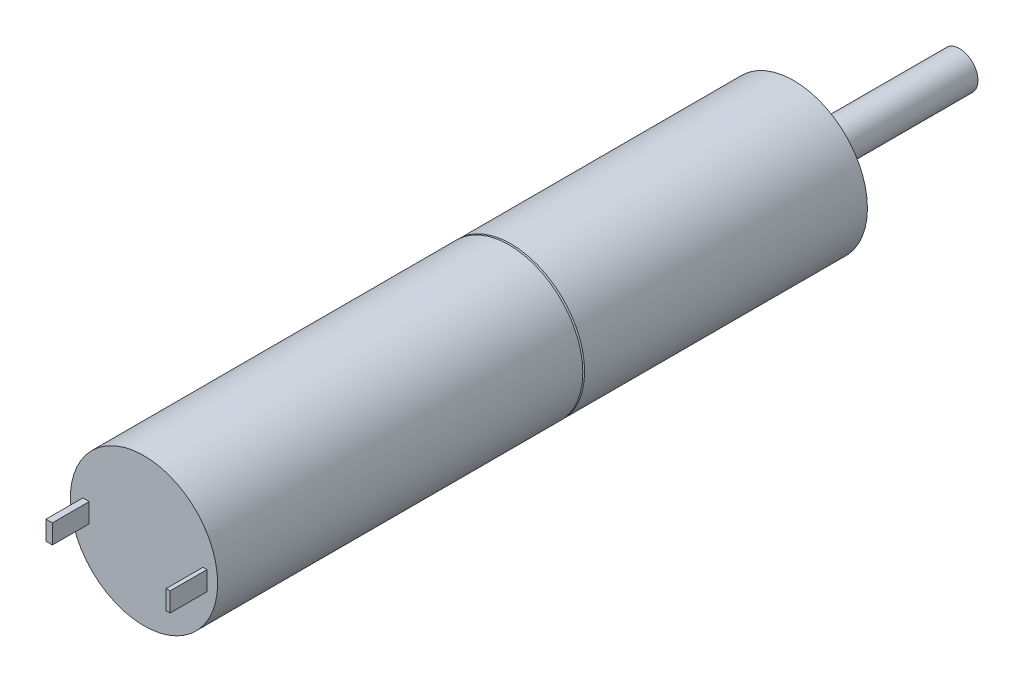
SolidWorks part; units mm, degrees
ref_plane "Front Plane" through (0, 0, 0) normal (0, 0, 1) x (1, 0, 0)
ref_plane "Top Plane" through (0, 0, 0) normal (0, 1, 0) x (1, 0, 0)
ref_plane "Right Plane" through (0, 0, 0) normal (1, 0, 0) x (0, 0, -1)
sketch "Sketch1" plane through (0, 0, 0) normal (0, 0, 1) x (1, 0, 0)
  circle A0 centre (0, 0) radius 6
  dimension "D1" = 12
extrude "Extrude1" add sketch "Sketch1" along normal blind 29.8 and the other way blind 23.1
sketch "Sketch2" plane through (0, 0, 29.8) normal (0, 0, 1) x (1, 0, 0)
  line L1 (4.8087, 0.5355) -> (5.1308, 0.5355)
  line L2 (4.8087, 0.5355) -> (4.8087, -1.0284)
  line L3 (4.8087, -1.0284) -> (5.1308, -1.0284)
  line L4 (5.1308, 0.5355) -> (5.1308, -1.0284)
  line L5 (-4.9748, 0.5355) -> (-4.4551, 0.5355)
  line L6 (-4.9748, 0.5355) -> (-4.9748, -1.0284)
  line L7 (-4.9748, -1.0284) -> (-4.4551, -1.0284)
  line L8 (-4.4551, 0.5355) -> (-4.4551, -1.0284)
extrude "Extrude2" add sketch "Sketch2" along normal blind 3
sketch "Sketch3" plane through (0, 0, -23.1) normal (0, 0, -1) x (-1, 0, 0)
  circle A0 centre (0, 0) radius 1.5
  dimension "D1" = 3
extrude "Extrude3" add sketch "Sketch3" along normal blind 13.5
sketch "Sketch4" plane through (0, 0, -23.1) normal (0, 0, -1) x (-1, 0, 0)
  line L0 (-4.75, 0) -> (4.75, 0) construction
  circle A0 centre (4.75, 0) radius 1
  circle A1 centre (-4.75, 0) radius 1
  point P4 (0, 0)
  dimension "D1" = 2
  dimension "D2" = 2
  dimension "D3" = 9.5
extrude "Cut-Extrude1" cut sketch "Sketch4" against normal blind 13.5
sketch "Sketch6" plane through (0, 0, 0) normal (1, 0, 0) x (0, 0, -1)
  line L1 (0, 5.8) -> (0.7148, 7.764)
  line L2 (0.7148, 7.764) -> (-0.7148, 7.764)
  line L3 (-0.7148, 7.764) -> (0, 5.8)
  line L4 (23.1, 6) -> (-29.8, 6) construction
  line L5 (0, 0) -> (-5.8629, 0) construction
  dimension "D1" = 0.2
revolve "Cut-Revolve1" cut sketch "Sketch6" angle 360 about L5
